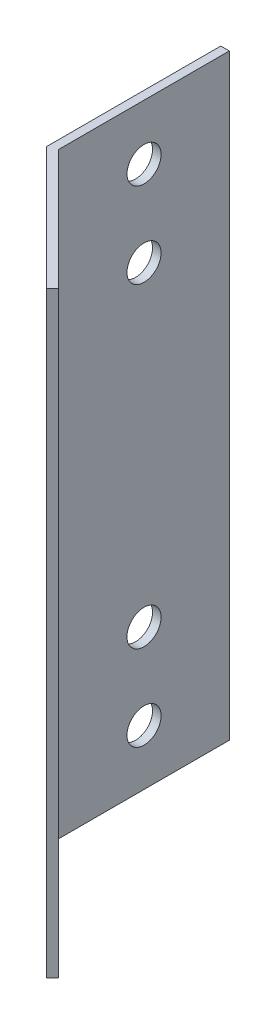
SolidWorks part; units mm, degrees
ref_plane "Face" through (0, 0, 0) normal (0, 0, 1) x (1, 0, 0)
ref_plane "Dessus" through (0, 0, 0) normal (0, 1, 0) x (1, 0, 0)
ref_plane "Droite" through (0, 0, 0) normal (1, 0, 0) x (0, 0, -1)
sketch "Esquisse1" plane through (0, 0, 0) normal (0, 1, 0) x (1, 0, 0)
  line L0 (0, 0) -> (0, 20.4142)
  line L1 (0, 20.4142) -> (1, 20.4142)
  line L2 (1, 20.4142) -> (1, 0.4142)
  line L3 (1, 0.4142) -> (15.1421, -13.7279)
  line L4 (15.1421, -13.7279) -> (14.435, -14.435)
  line L5 (14.435, -14.435) -> (0, 0)
  dimension "D1" = 1
  dimension "D2" = 1
  dimension "D3" = 45
  dimension "D4" = 20
extrude "Extrusion1" add sketch "Esquisse1" along normal blind 70
sketch "Esquisse2" plane through (1, 0, 0) normal (1, 0, 0) x (0, 0, -1)
  line L0 (0.4142, 35) -> (20.4142, 35) construction
  line L1 (0.4142, 70) -> (0.4142, 0) construction
  line L2 (20.4142, 70) -> (20.4142, 0) construction
  line L3 (10.4142, 0) -> (10.4142, 70) construction
  line L4 (0.4142, 0) -> (20.4142, 0) construction
  line L5 (0.4142, 70) -> (20.4142, 70) construction
  circle A0 centre (10.4142, 16.5) radius 2
  circle A1 centre (10.4142, 6.5) radius 2
  circle A2 centre (10.4142, 53.5) radius 2
  circle A3 centre (10.4142, 63.5) radius 2
  dimension "D1" = 4
  dimension "D2" = 18.5
  dimension "D3" = 10
extrude "Extrusion2" cut sketch "Esquisse2" against normal up to next
sketch "Esquisse3" plane through (0.7071, 0, -0.7071) normal (0.7071, 0, -0.7071) x (-0.7071, 0, -0.7071)
  line L0 (-10.4142, 70) -> (-10.4142, 0) construction
  line L1 (-20.4142, 70) -> (-0.4142, 70) construction
  line L2 (-20.4142, 0) -> (-0.4142, 0) construction
  line L3 (-20.4142, 35) -> (-0.4142, 35) construction
  line L4 (-20.4142, 70) -> (-20.4142, 0) construction
  line L5 (-0.4142, 70) -> (-0.4142, 0) construction
  circle A0 centre (-10.4142, 53.5) radius 2
  circle A1 centre (-10.4142, 63.5) radius 2
  circle A2 centre (-10.4142, 6.5) radius 2
  circle A3 centre (-10.4142, 16.5) radius 2
  dimension "D1" = 4
  dimension "D2" = 18.5
  dimension "D3" = 10
extrude "Extrusion3" cut sketch "Esquisse3" against normal up to next
